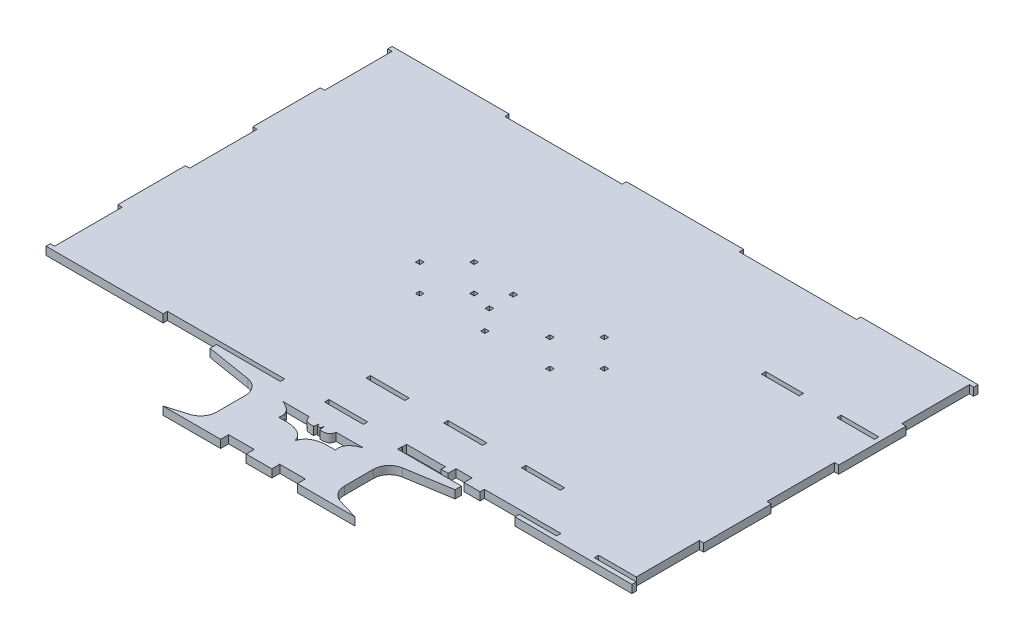
SolidWorks part; units mm, degrees
ref_plane "Front Plane" through (0, 0, 0) normal (0, 0, 1) x (1, 0, 0)
ref_plane "Top Plane" through (0, 0, 0) normal (0, 1, 0) x (1, 0, 0)
ref_plane "Right Plane" through (0, 0, 0) normal (1, 0, 0) x (0, 0, -1)
sketch "Sketch1" plane through (0, 0, 0) normal (0, 1, 0) x (1, 0, 0)
  line L0 (-183.2, 108.2) -> (-109.92, 108.2)
  line L1 (-109.92, 105.5) -> (-36.64, 105.5)
  line L4 (180.5, 105.5) -> (180.5, 63.3)
  line L5 (183.2, 108.2) -> (183.2, 105.5)
  line L8 (183.2, 63.3) -> (183.2, 21.1)
  line L9 (183.2, 108.2) -> (183.2, -108.2) construction
  line L10 (180.5, -105.5) -> (183.2, -105.5)
  line L11 (180.5, 105.5) -> (183.2, 105.5)
  line L13 (180.5, 105.5) -> (180.5, -105.5) construction
  line L14 (180.5, 21.1) -> (180.5, -21.1)
  line L16 (180.5, -63.3) -> (180.5, -102.8)
  line L18 (-180.5, 105.5) -> (-180.5, -105.5) construction
  line L23 (-183.2, 108.2) -> (183.2, 108.2) construction
  line L24 (-36.64, 108.2) -> (36.64, 108.2)
  line L26 (109.92, 108.2) -> (183.2, 108.2)
  line L27 (-109.92, 108.2) -> (-109.92, 105.5)
  line L28 (-36.64, 108.2) -> (-36.64, 105.5)
  line L29 (36.64, 108.2) -> (36.64, 105.5)
  line L30 (109.92, 108.2) -> (109.92, 105.5)
  line L31 (-180.5, 105.5) -> (180.5, 105.5) construction
  line L32 (36.64, 105.5) -> (109.92, 105.5)
  line L33 (-183.2, -108.2) -> (183.2, -108.2) construction
  line L34 (-180.5, -105.5) -> (180.5, -105.5) construction
  line L35 (180.5, -21.1) -> (183.2, -21.1)
  line L36 (109.92, -108.2) -> (183.2, -108.2)
  line L37 (109.92, -108.2) -> (109.92, -105.5)
  line L38 (36.64, -105.5) -> (36.9, -105.5)
  line L39 (36.64, -108.2) -> (36.64, -105.5)
  line L41 (-36.64, -108.2) -> (-36.64, -105.5)
  line L42 (-109.92, -105.5) -> (-36.64, -105.5)
  line L43 (-109.92, -108.2) -> (-109.92, -105.5)
  line L44 (-183.2, -108.2) -> (-109.92, -108.2)
  line L45 (180.5, -63.3) -> (183.2, -63.3)
  line L46 (180.5, 21.1) -> (183.2, 21.1)
  line L47 (180.5, 63.3) -> (183.2, 63.3)
  line L48 (183.2, -21.1) -> (183.2, -63.3)
  line L49 (-183.2, 108.2) -> (-183.2, -108.2) construction
  line L50 (183.2, -105.5) -> (183.2, -108.2)
  line L51 (-40, -126.6956) -> (-40, -144.7597)
  line L52 (-183.2, -105.5) -> (-183.2, -108.2)
  line L53 (-180.5, -105.5) -> (-183.2, -105.5)
  line L54 (-180.5, -63.3) -> (-180.5, -105.5)
  line L55 (-180.5, -63.3) -> (-183.2, -63.3)
  line L56 (-183.2, -21.1) -> (-183.2, -63.3)
  line L57 (-180.5, -21.1) -> (-183.2, -21.1)
  line L58 (-180.5, 21.1) -> (-180.5, -21.1)
  line L59 (-180.5, 21.1) -> (-183.2, 21.1)
  line L60 (-183.2, 63.3) -> (-183.2, 21.1)
  line L61 (-180.5, 63.3) -> (-183.2, 63.3)
  line L62 (-180.5, 105.5) -> (-180.5, 63.3)
  line L63 (-183.2, 108.2) -> (-183.2, 105.5)
  line L64 (-180.5, 105.5) -> (-183.2, 105.5)
  line L67 (40, -126.6956) -> (40, -144.7597)
  line L70 (-40, -158.2) -> (-24, -158.2)
  line L71 (24, -153.2) -> (8, -153.2)
  line L75 (-8, -158.2) -> (8, -158.2)
  line L77 (24, -158.2) -> (40, -158.2)
  line L78 (-24, -158.2) -> (-24, -153.2)
  line L79 (-8, -158.2) -> (-8, -153.2)
  line L80 (8, -158.2) -> (8, -153.2)
  line L81 (24, -158.2) -> (24, -153.2)
  line L82 (-8, -153.2) -> (-24, -153.2)
  line L83 (-36.64, -108.2) -> (-76.64, -108.2)
  line L84 (36.64, -108.2) -> (76.64, -108.2)
  line L85 (-76.64, -108.2) -> (-76.64, -112.2)
  line L86 (-76.64, -112.2) -> (-48.384, -116.8271)
  line L87 (76.64, -108.2) -> (76.64, -112.2)
  line L88 (76.64, -112.2) -> (48.384, -116.8271)
  line L89 (-40, -158.2) -> (-60, -158.2)
  line L90 (40, -158.2) -> (60, -158.2)
  line L92 (-47.1265, -154.338) -> (-60, -158.2)
  line L94 (47.1265, -154.338) -> (60, -158.2)
  line L95 (0.9301, -120.7166) -> (0, -120.6808)
  line L196 (1.4468, -118.9339) -> (0.9301, -120.7166)
  line L197 (25.0098, -118.2105) -> (8.3452, -118.288)
  line L198 (1.5053, -118.7321) -> (1.5244, -118.908)
  line L199 (1.5053, -118.7321) -> (1.4468, -118.9339)
  line L200 (-1.5053, -118.7321) -> (-1.4468, -118.9339)
  line L201 (-1.5053, -118.7321) -> (-1.5244, -118.908)
  line L202 (-25.0098, -118.2105) -> (-8.3452, -118.288)
  line L203 (-1.4468, -118.9339) -> (-0.9301, -120.7166)
  line L204 (-0.9301, -120.7166) -> (0, -120.6808)
  line L205 (56.3537, 1.35) -> (56.3537, -1.35)
  line L206 (56.3537, -1.35) -> (59.0537, -1.35)
  line L207 (59.0537, -1.35) -> (59.0537, 1.35)
  line L208 (59.0537, 1.35) -> (56.3537, 1.35)
  line L209 (39.3537, 18.35) -> (39.3537, 15.65)
  line L210 (39.3537, 15.65) -> (42.0537, 15.65)
  line L211 (42.0537, 15.65) -> (42.0537, 18.35)
  line L212 (42.0537, 18.35) -> (39.3537, 18.35)
  line L213 (39.3537, -15.65) -> (39.3537, -18.35)
  line L214 (39.3537, -18.35) -> (42.0537, -18.35)
  line L215 (42.0537, -18.35) -> (42.0537, -15.65)
  line L216 (42.0537, -15.65) -> (39.3537, -15.65)
  line L217 (22.3537, 1.35) -> (22.3537, -1.35)
  line L218 (22.3537, -1.35) -> (25.0537, -1.35)
  line L219 (25.0537, -1.35) -> (25.0537, 1.35)
  line L220 (25.0537, 1.35) -> (22.3537, 1.35)
  line L221 (-25.0537, 1.35) -> (-22.3537, 1.35)
  line L223 (-25.0537, -1.35) -> (-25.0537, 1.35)
  line L224 (-22.3537, -1.35) -> (-25.0537, -1.35)
  line L225 (-22.3537, 1.35) -> (-22.3537, -1.35)
  line L226 (-42.0537, -15.65) -> (-39.3537, -15.65)
  line L227 (-42.0537, -18.35) -> (-42.0537, -15.65)
  line L228 (-39.3537, -18.35) -> (-42.0537, -18.35)
  line L229 (-39.3537, -15.65) -> (-39.3537, -18.35)
  line L230 (-42.0537, 18.35) -> (-39.3537, 18.35)
  line L231 (-42.0537, 15.65) -> (-42.0537, 18.35)
  line L232 (-39.3537, 15.65) -> (-42.0537, 15.65)
  line L233 (-39.3537, 18.35) -> (-39.3537, 15.65)
  line L234 (-59.0537, 1.35) -> (-56.3537, 1.35)
  line L235 (-59.0537, -1.35) -> (-59.0537, 1.35)
  line L236 (-56.3537, -1.35) -> (-59.0537, -1.35)
  line L237 (-56.3537, 1.35) -> (-56.3537, -1.35)
  line L250 (1.3481, -18.3469) -> (1.3481, -15.6469)
  line L262 (156.9333, -102.8) -> (180.5, -102.8)
  line L263 (-1.3519, -18.3469) -> (1.3481, -18.3469)
  line L264 (-1.3519, -15.6469) -> (-1.3519, -18.3469)
  line L265 (1.3481, -15.6469) -> (-1.3519, -15.6469)
  line L266 (-9.5244, 10.3029) -> (-9.5244, 13.0029)
  line L267 (-12.2244, 10.3029) -> (-9.5244, 10.3029)
  line L268 (-12.2244, 13.0029) -> (-12.2244, 10.3029)
  line L269 (-9.5244, 13.0029) -> (-12.2244, 13.0029)
  line L270 (-9.5244, -4.6971) -> (-9.5244, -1.9971)
  line L271 (-12.2244, -4.6971) -> (-9.5244, -4.6971)
  line L272 (-12.2244, -1.9971) -> (-12.2244, -4.6971)
  line L273 (-9.5244, -1.9971) -> (-12.2244, -1.9971)
  line L274 (180.5, -105.5) -> (156.9333, -105.5)
  line L275 (70.5, -100.5) -> (65.5, -100.5)
  line L276 (65.5, -100.5) -> (65.5, -105.5)
  line L277 (70.5, -100.5) -> (75.5, -100.5)
  line L278 (75.5, -100.5) -> (75.5, -105.5)
  line L279 (75.5, -105.5) -> (85.5, -105.5)
  line L281 (180.5, 48.9) -> (156.9333, 48.9)
  line L283 (180.5, 46.2) -> (156.9333, 46.2)
  line L284 (133.3667, 48.9) -> (109.8, 48.9)
  line L285 (109.8, -79.6) -> (109.8, -76.9)
  line L286 (180.5, 48.9) -> (180.5, 46.2)
  line L287 (133.3667, 48.9) -> (133.3667, 46.2)
  line L288 (109.8, 48.9) -> (109.8, 46.2)
  line L289 (156.9333, 48.9) -> (156.9333, 46.2)
  line L290 (109.8, -102.8) -> (133.3667, -102.8)
  line L291 (156.9333, -105.5) -> (156.9333, -102.8)
  line L292 (133.3667, -105.5) -> (133.3667, -102.8)
  line L293 (133.3667, 46.2) -> (109.8, 46.2)
  line L294 (133.3667, -105.5) -> (109.92, -105.5)
  line L296 (109.8, -76.9) -> (85.5, -76.9)
  line L297 (12.6, -105.5) -> (-11.7, -105.5)
  line L298 (-11.7, -79.6) -> (-11.7, -76.9)
  line L299 (109.8, -105.5) -> (109.8, -76.9) construction
  line L300 (107.1, -79.6) -> (85.5, -79.6)
  line L301 (12.6, -79.6) -> (-9, -79.6)
  line L302 (-9, -102.8) -> (12.6, -102.8)
  line L303 (107.1, -105.5) -> (107.1, -79.6) construction
  line L304 (109.8, -76.9) -> (-11.7, -76.9) construction
  line L305 (61.2, -76.9) -> (36.9, -76.9)
  line L306 (61.2, -79.6) -> (36.9, -79.6)
  line L307 (12.6, -76.9) -> (-11.7, -76.9)
  line L308 (12.6, -76.9) -> (12.6, -79.6)
  line L309 (36.9, -76.9) -> (36.9, -79.6)
  line L310 (61.2, -76.9) -> (61.2, -79.6)
  line L311 (85.5, -76.9) -> (85.5, -79.6)
  line L312 (107.1, -79.6) -> (109.8, -79.6)
  line L313 (85.5, -105.5) -> (85.5, -102.8)
  line L314 (61.2, -105.5) -> (61.2, -102.8)
  line L315 (36.9, -105.5) -> (36.9, -102.8)
  line L316 (12.6, -105.5) -> (12.6, -102.8)
  line L317 (36.64, -102.8) -> (-9, -102.8) construction
  line L318 (-9, -79.6) -> (-11.7, -79.6)
  line L319 (-11.7, -105.5) -> (-11.7, -76.9) construction
  line L320 (-9, -102.8) -> (-9, -79.6) construction
  line L321 (107.1, -79.6) -> (-9, -79.6) construction
  line L322 (85.5, -102.8) -> (109.8, -102.8)
  line L323 (61.2, -105.5) -> (65.5, -105.5)
  line L324 (36.9, -102.8) -> (61.2, -102.8)
  line L325 (36.64, -105.5) -> (-11.7, -105.5) construction
  line L326 (-11.7, -105.5) -> (-11.7, -102.8)
  line L327 (-11.7, -102.8) -> (-9, -102.8)
  arc A0 (-48.384, -116.8271) -> (-40, -126.6956) centre (-50, -126.6956) cw
  arc A1 (40, -126.6956) -> (48.384, -116.8271) centre (50, -126.6956) cw
  arc A2 (-47.1265, -154.338) -> (-40, -144.7597) centre (-50, -144.7597) ccw
  arc A3 (40, -144.7597) -> (47.1265, -154.338) centre (50, -144.7597) ccw
  spline S0 degree 3 poles (0, -135.7277) (-0.2584, -135.0818) (-0.4466, -134.4031) (-0.7751, -133.7899) (-1.0966, -133.1898) (-1.4897, -132.6232) (-1.9377, -132.1105) (-2.391, -131.5919) (-2.9056, -131.1213) (-3.4621, -130.7154) (-4.0576, -130.281) (-4.6993, -129.9012) (-5.374, -129.6044) (-6.2141, -129.2348) (-7.0911, -128.9401) (-7.9835, -128.7259) (-9.0354, -128.4735) (-10.1097, -128.3041) (-11.1872, -128.2092) (-12.586, -128.0861) (-13.9951, -128.0606) (-15.3986, -128.1059) (-16.1735, -128.1309) (-16.9488, -128.1403) (-17.7239, -128.1575) knots 0 0 0 0 1 1 1 2 2 2 3 3 3 4 4 4 5 5 5 6 6 6 7 7 7 8 8 8 8
  spline S1 degree 3 poles (-17.7239, -128.1575) (-17.6464, -127.503) (-17.4868, -126.853) (-17.4914, -126.194) (-17.4955, -125.602) (-17.5727, -125.0019) (-17.7497, -124.4371) (-17.9387, -123.8343) (-18.2232, -123.2555) (-18.5765, -122.7319) (-18.9621, -122.1603) (-19.4328, -121.6422) (-19.9459, -121.1817) (-20.533, -120.6546) (-21.1783, -120.1875) (-21.8578, -119.7865) (-22.8694, -119.1894) (-23.9755, -118.7674) (-25.0098, -118.2105) knots 0 0 0 0 1 1 1 2 2 2 3 3 3 4 4 4 5 5 5 6 6 6 6
  spline S2 degree 3 poles (2.0928, -122.1118) (2.0066, -121.9998) (1.8591, -121.915) (1.8344, -121.7759) (1.6664, -120.8292) (1.6277, -119.864) (1.5244, -118.908) knots 0 0 0 0 1 1 1 2 2 2 2
  spline S3 degree 3 poles (8.3452, -118.288) (8.173, -118.8564) (8.0758, -119.4532) (7.8285, -119.9932) (7.6484, -120.3864) (7.396, -120.758) (7.0792, -121.0525) (6.7709, -121.3391) (6.397, -121.5764) (5.9941, -121.6984) (5.1566, -121.952) (4.2806, -122.0712) (3.4104, -122.1635) (2.9733, -122.2098) (2.532, -122.129) (2.0928, -122.1118) knots 0 0 0 0 1 1 1 2 2 2 3 3 3 4 4 4 5 5 5 5
  spline S4 degree 3 poles (17.7239, -128.1575) (17.6464, -127.503) (17.4868, -126.853) (17.4914, -126.194) (17.4955, -125.602) (17.5727, -125.0019) (17.7497, -124.4371) (17.9387, -123.8343) (18.2232, -123.2555) (18.5765, -122.7319) (18.9621, -122.1603) (19.4328, -121.6422) (19.9459, -121.1817) (20.533, -120.6546) (21.1783, -120.1875) (21.8578, -119.7865) (22.8694, -119.1894) (23.9755, -118.7674) (25.0098, -118.2105) knots 0 0 0 0 1 1 1 2 2 2 3 3 3 4 4 4 5 5 5 6 6 6 6
  spline S5 degree 3 poles (-8.3452, -118.288) (-8.173, -118.8564) (-8.0758, -119.4532) (-7.8285, -119.9932) (-7.6484, -120.3864) (-7.396, -120.758) (-7.0792, -121.0525) (-6.7709, -121.3391) (-6.397, -121.5764) (-5.9941, -121.6984) (-5.1566, -121.952) (-4.2806, -122.0712) (-3.4104, -122.1635) (-2.9733, -122.2098) (-2.532, -122.129) (-2.0928, -122.1118) knots 0 0 0 0 1 1 1 2 2 2 3 3 3 4 4 4 5 5 5 5
  spline S6 degree 3 poles (-2.0928, -122.1118) (-2.0066, -121.9998) (-1.8591, -121.915) (-1.8344, -121.7759) (-1.6664, -120.8292) (-1.6277, -119.864) (-1.5244, -118.908) knots 0 0 0 0 1 1 1 2 2 2 2
  spline S7 degree 3 poles (0, -135.7277) (0.2584, -135.0818) (0.4466, -134.4031) (0.7751, -133.7899) (1.0966, -133.1898) (1.4897, -132.6232) (1.9377, -132.1105) (2.391, -131.5919) (2.9056, -131.1213) (3.4621, -130.7154) (4.0576, -130.281) (4.6993, -129.9012) (5.374, -129.6044) (6.2141, -129.2348) (7.0911, -128.9401) (7.9835, -128.7259) (9.0354, -128.4735) (10.1097, -128.3041) (11.1872, -128.2092) (12.586, -128.0861) (13.9951, -128.0606) (15.3986, -128.1059) (16.1735, -128.1309) (16.9488, -128.1403) (17.7239, -128.1575) knots 0 0 0 0 1 1 1 2 2 2 3 3 3 4 4 4 5 5 5 6 6 6 7 7 7 8 8 8 8
  point P0 (0, 0)
  point P58 (-40, -118.2)
  point P68 (40, -118.2)
  point P78 (0, 0)
  dimension "D2" = 10
  dimension "D3" = 10
  dimension "D6" = 10
  dimension "D7" = 10
  dimension "D1" = 2.7
  dimension "D4" = 40
  dimension "D5" = 40
  dimension "D8" = 70.7
  dimension "D9" = 154.4
  dimension "D10" = 2.7
extrude "Boss-Extrude1" add sketch "Sketch1" along normal blind 5
